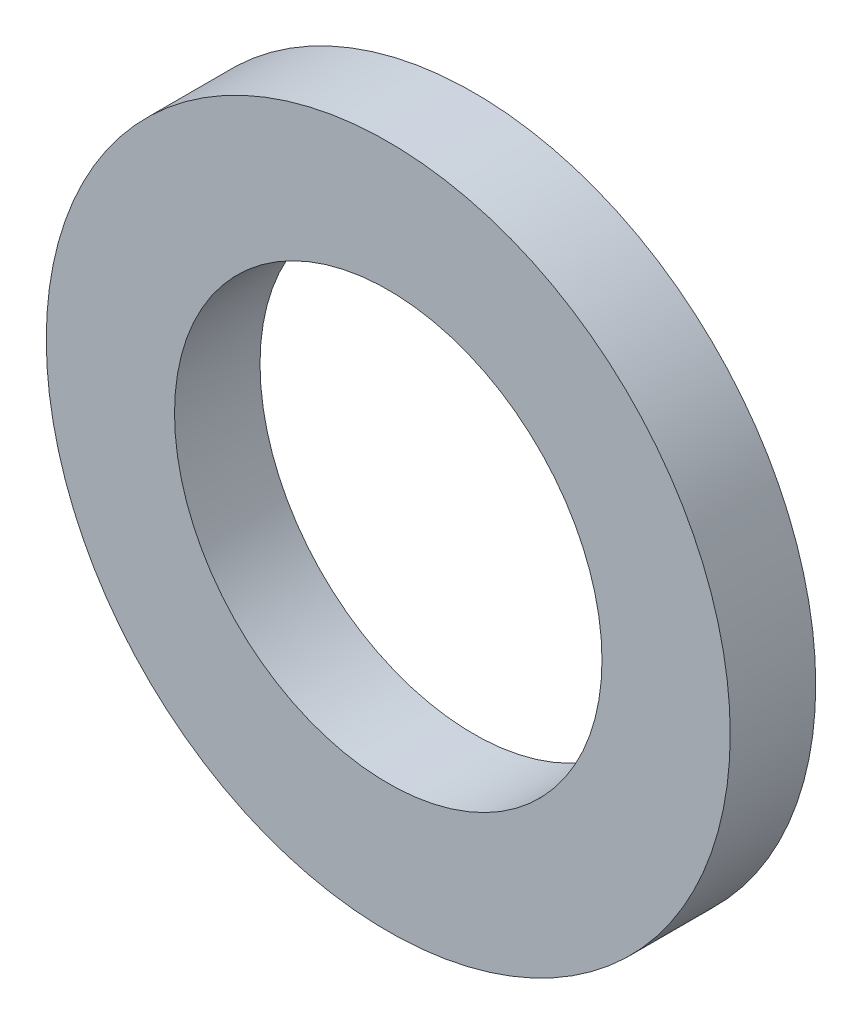
SolidWorks part; units mm, degrees
ref_plane "Front Plane" through (0, 0, 0) normal (0, 0, 1) x (1, 0, 0)
ref_plane "Top Plane" through (0, 0, 0) normal (0, 1, 0) x (1, 0, 0)
ref_plane "Right Plane" through (0, 0, 0) normal (1, 0, 0) x (0, 0, -1)
sketch "Sketch1" plane through (0, 0, 0) normal (0, 0, 1) x (1, 0, 0)
  circle A0 centre (0, 0) radius 2.5
  circle A1 centre (0, 0) radius 4
extrude "Boss-Extrude1" add sketch "Sketch1" along normal blind 1
